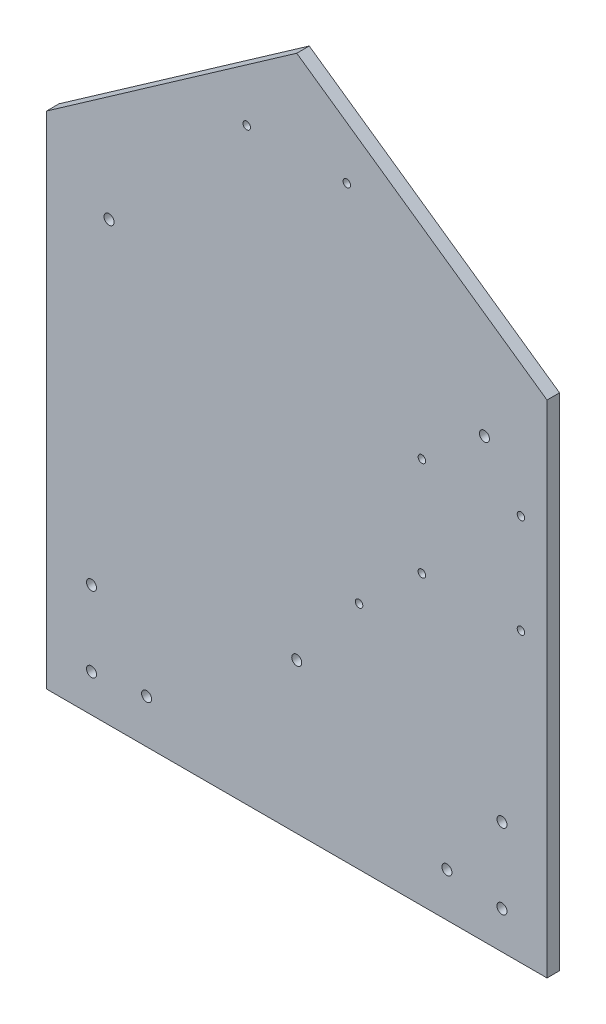
SolidWorks part; units mm, degrees
ref_plane "Front Plane" through (0, 0, 0) normal (0, 0, 1) x (1, 0, 0)
ref_plane "Top Plane" through (0, 0, 0) normal (0, 1, 0) x (1, 0, 0)
ref_plane "Right Plane" through (0, 0, 0) normal (1, 0, 0) x (0, 0, -1)
sketch "Sketch1" plane through (0, 0, 0) normal (0, 0, 1) x (1, 0, 0)
  line L0 (7.503, 174.8718) -> (7.503, 4.8718) construction
  line L2 (-92.497, 104.8718) -> (-92.497, -95.1282)
  line L3 (-92.497, -95.1282) -> (107.503, -95.1282)
  line L4 (107.503, 104.8718) -> (107.503, -95.1282)
  line L5 (-92.497, 104.8718) -> (107.503, -95.1282) construction
  line L6 (-92.497, -95.1282) -> (107.503, 104.8718) construction
  line L7 (7.503, 139.8718) -> (43.7806, 139.8718) construction
  line L8 (-92.497, 104.8718) -> (7.503, 174.8718)
  line L9 (7.503, 174.8718) -> (107.503, 104.8718)
  line L10 (107.503, 104.8718) -> (-92.497, 104.8718) construction
  line L11 (7.503, 4.8718) -> (7.503, -95.1282) construction
  line L12 (-39.3325, -3.1282) -> (46.494, -3.1282) construction
  line L13 (134.6551, 39.6718) -> (-21.6361, 39.6718) construction
  line L14 (7.503, 4.8718) -> (215.7254, 4.8718) construction
  line L15 (77.303, 53.8857) -> (77.303, 31.8895) construction
  circle A0 centre (89.503, -80.1282) radius 2
  circle A1 centre (-74.497, -80.1282) radius 2
  circle A2 centre (27.503, 139.8718) radius 1.5
  circle A5 centre (-12.497, 139.8718) radius 1.5
  circle A6 centre (89.503, -50.1282) radius 2
  circle A7 centre (-74.497, -50.1282) radius 2
  circle A8 centre (7.503, -35.1282) radius 2
  circle A9 centre (32.403, -3.1282) radius 1.5
  circle A12 centre (57.503, 19.8718) radius 1.5
  circle A13 centre (-52.497, -77.6282) radius 2
  circle A14 centre (67.503, -77.6282) radius 2
  circle A15 centre (-67.497, 79.8718) radius 2
  circle A16 centre (82.503, 79.8718) radius 2
  circle A17 centre (57.503, 59.4718) radius 1.5
  circle A18 centre (97.103, 19.8718) radius 1.5
  circle A19 centre (97.103, 59.4718) radius 1.5
  point P0 (7.503, 4.8718)
  dimension "D4" = 4
  dimension "D7" = 4
  dimension "D11" = 3
  dimension "D13" = 4
  dimension "D16" = 3
  dimension "D18" = 4
  dimension "D21" = 4
  dimension "D24" = 3
  dimension "D1" = 200
  dimension "D2" = 200
  dimension "D3" = 170
  dimension "D5" = 18
  dimension "D6" = 15
  dimension "D8" = 18
  dimension "D9" = 45
  dimension "D10" = 35
  dimension "D12" = 20
  dimension "D14" = 40
  dimension "D15" = 8
  dimension "D17" = 24.9
  dimension "D19" = 82.5
  dimension "D20" = 60
  dimension "D22" = 75
  dimension "D23" = 75
  dimension "D25" = 50
  dimension "D26" = 15
  dimension "D27" = 34.8
  dimension "D28" = 69.8
extrude "Boss-Extrude1" add sketch "Sketch1" along normal blind 5
